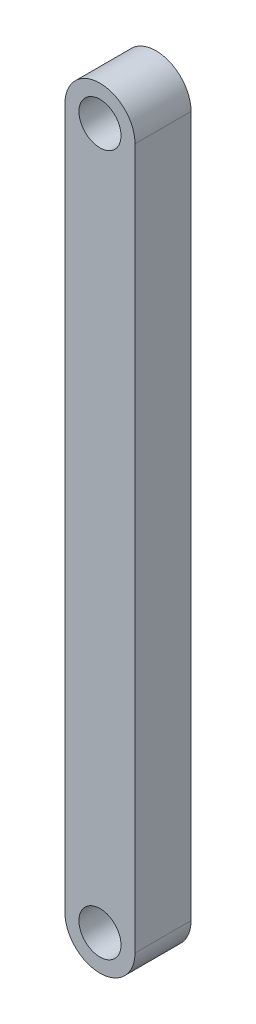
SolidWorks part; units mm, degrees
ref_plane "Front Plane" through (0, 0, 0) normal (0, 0, 1) x (1, 0, 0)
ref_plane "Top Plane" through (0, 0, 0) normal (0, 1, 0) x (1, 0, 0)
ref_plane "Right Plane" through (0, 0, 0) normal (1, 0, 0) x (0, 0, -1)
sketch "Sketch1" plane through (0, 0, 0) normal (0, 0, 1) x (1, 0, 0)
  line L0 (0, -125) -> (0, 125) construction
  line L1 (-12.5, -125) -> (-12.5, 125)
  line L2 (12.5, -125) -> (12.5, 125)
  arc A0 (-12.5, -125) -> (12.5, -125) centre (0, -125) ccw
  arc A1 (12.5, 125) -> (-12.5, 125) centre (0, 125) ccw
  circle A2 centre (0, 125) radius 7.5
  circle A3 centre (0, -125) radius 7.5
  point P3 (0, 0)
  dimension "D3" = 15
  dimension "D1" = 25
  dimension "D2" = 250
extrude "Boss-Extrude1" add sketch "Sketch1" along normal blind 20
